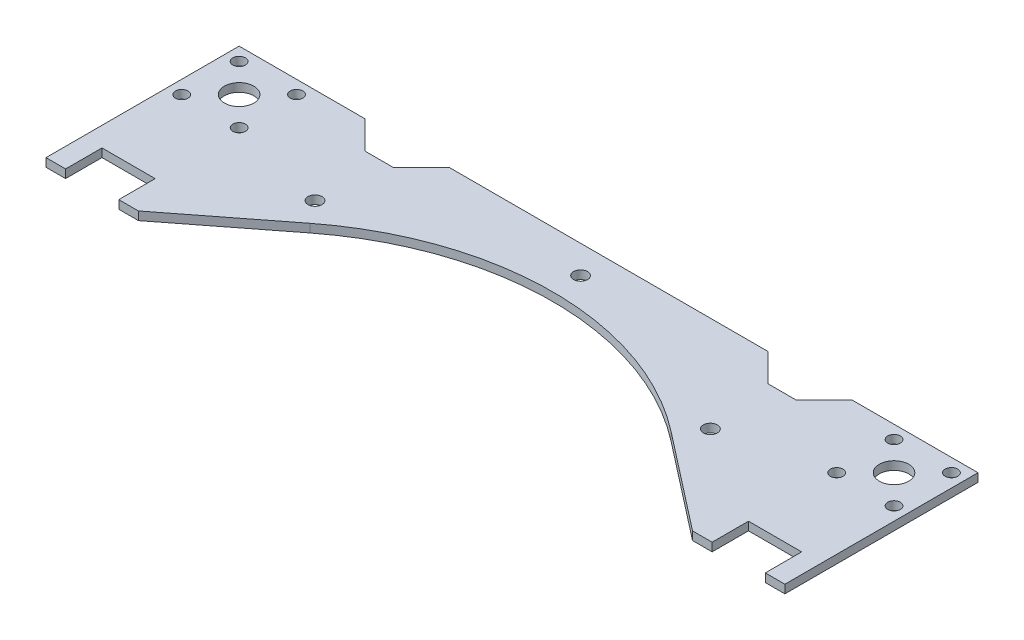
SolidWorks part; units mm, degrees
ref_plane "Face" through (0, 0, 0) normal (0, 0, 1) x (1, 0, 0)
ref_plane "Dessus" through (0, 0, 0) normal (0, 1, 0) x (1, 0, 0)
ref_plane "Droite" through (0, 0, 0) normal (1, 0, 0) x (0, 0, -1)
sketch "Esquisse1" plane through (0, 0, 0) normal (0, 1, 0) x (1, 0, 0)
  line L0 (0, 0) -> (0, 372.8366) construction
  line L1 (0, 0) -> (0, -232.7616) construction
  line L2 (558.5742, 0) -> (-497.8331, 0) construction
  line L3 (-64.4944, 52.8582) -> (-99, 26)
  line L4 (-132, 26) -> (-125, 26)
  line L5 (-132, 26) -> (-132, 95)
  line L6 (-132, 95) -> (-87, 95)
  line L7 (132, 26) -> (132, 95)
  line L8 (-132, 26) -> (-99, 26) construction
  line L9 (64.4944, 52.8582) -> (99, 26)
  line L10 (-87, 95) -> (-77, 85)
  line L11 (-77, 85) -> (-67, 85)
  line L12 (-67, 85) -> (-57, 95)
  line L13 (-57, 95) -> (57, 95)
  line L14 (67, 85) -> (57, 95)
  line L15 (77, 85) -> (67, 85)
  line L16 (132, 95) -> (87, 95)
  line L17 (87, 95) -> (77, 85)
  line L18 (-132, 80) -> (-117, 80) construction
  line L19 (-117, 80) -> (-117, 95) construction
  line L20 (-125, 26) -> (-125, 39)
  line L21 (-125, 39) -> (-106, 39)
  line L22 (-106, 39) -> (-106, 26)
  line L23 (-106, 26) -> (-99, 26)
  line L24 (-115.5, 26) -> (-115.5, 39) construction
  line L25 (132, 26) -> (125, 26)
  line L26 (125, 26) -> (125, 39)
  line L27 (125, 39) -> (106, 39)
  line L28 (106, 39) -> (106, 26)
  line L29 (106, 26) -> (99, 26)
  line L30 (-127.253, 80) -> (-127.253, 90.253) construction
  line L31 (-127.253, 90.253) -> (-117, 90.253) construction
  line L32 (-64.4944, 52.8582) -> (64.4944, 52.8582) construction
  line L33 (-64.4944, 52.8582) -> (-70.6367, 60.7494) construction
  arc A0 (64.4944, 52.8582) -> (-64.4944, 52.8582) centre (0, -30) ccw
  circle A1 centre (-117, 80) radius 5.25
  circle A2 centre (117, 80) radius 5.25
  circle A3 centre (-127.253, 90.253) radius 2.25
  circle A4 centre (-106.747, 90.253) radius 2.25
  circle A5 centre (-106.747, 69.747) radius 2.25
  circle A6 centre (-127.253, 69.747) radius 2.25
  circle A7 centre (106.747, 69.747) radius 2.25
  circle A8 centre (127.253, 69.747) radius 2.25
  circle A9 centre (127.253, 90.253) radius 2.25
  circle A10 centre (106.747, 90.253) radius 2.25
  circle A11 centre (-70.6367, 60.7494) radius 2.5
  circle A12 centre (70.6367, 60.7494) radius 2.5
  circle A13 centre (0, 85) radius 2.5
  point P3 (0, 75)
  point P21 (0, 95)
  dimension "D2" = 105
  dimension "D3" = 33
  dimension "D6" = 45
  dimension "D8" = 45
  dimension "D11" = 10.5
  dimension "D17" = 4.5
  dimension "D19" = 5
  dimension "D21" = 5
  dimension "D1" = 30
  dimension "D4" = 69
  dimension "D5" = 132
  dimension "D7" = 10
  dimension "D9" = 10
  dimension "D10" = 20
  dimension "D12" = 15
  dimension "D13" = 15
  dimension "D14" = 7
  dimension "D15" = 7
  dimension "D16" = 13
  dimension "D18" = 14.5
  dimension "D20" = 10
  dimension "D22" = 10
extrude "Extrusion1" add sketch "Esquisse1" along normal blind 3
